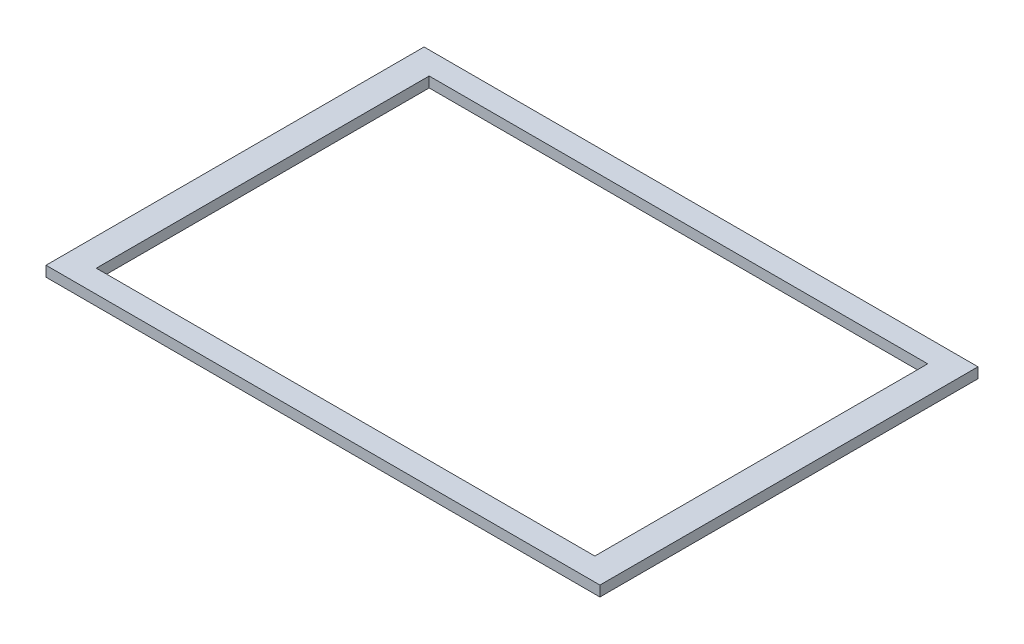
SolidWorks part; units mm, degrees
ref_plane "Front Plane" through (0, 0, 0) normal (0, 0, 1) x (1, 0, 0)
ref_plane "Top Plane" through (0, 0, 0) normal (0, 1, 0) x (1, 0, 0)
ref_plane "Right Plane" through (0, 0, 0) normal (1, 0, 0) x (0, 0, -1)
sketch "Sketch1" plane through (0, 0, 0) normal (0, 1, 0) x (1, 0, 0)
  line L1 (127, 86.6775) -> (-127, 86.6775)
  line L2 (127, 86.6775) -> (127, -86.6775)
  line L3 (127, -86.6775) -> (-127, -86.6775)
  line L4 (-127, 86.6775) -> (-127, -86.6775)
  line L5 (127, 86.6775) -> (-127, -86.6775) construction
  line L6 (127, -86.6775) -> (-127, 86.6775) construction
  line L7 (114.3, 76.327) -> (-114.3, 76.327)
  line L8 (114.3, 76.327) -> (114.3, -76.327)
  line L9 (114.3, -76.327) -> (-114.3, -76.327)
  line L10 (-114.3, 76.327) -> (-114.3, -76.327)
  line L11 (114.3, 76.327) -> (-114.3, -76.327) construction
  line L12 (114.3, -76.327) -> (-114.3, 76.327) construction
  point P0 (0, 0)
  point P6 (0, 0)
  dimension "D1" = 173.355
  dimension "D2" = 254
  dimension "D3" = 152.654
  dimension "D4" = 228.6
extrude "Boss-Extrude1" add sketch "Sketch1" along normal blind 4.7625
